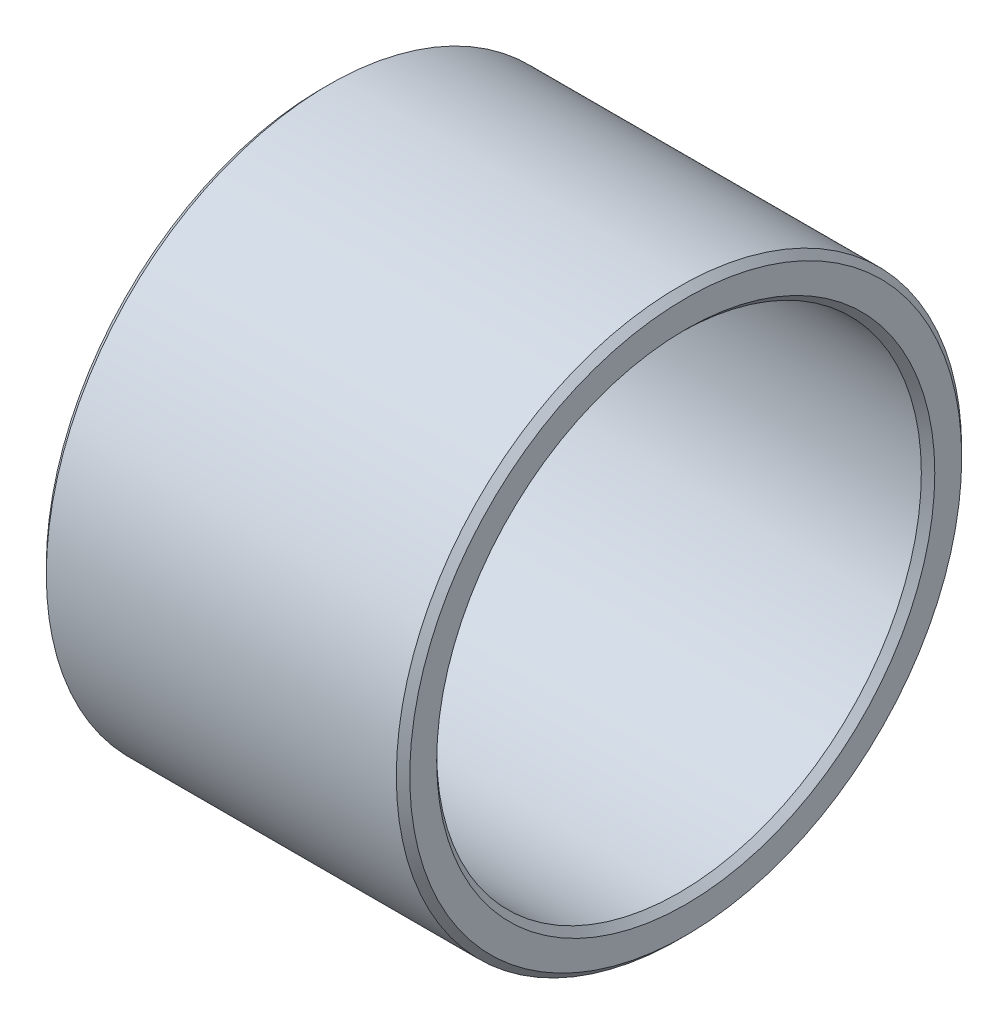
SolidWorks part; units mm, degrees
material "普通碳钢"
ref_plane "前视基准面" through (0, 0, 0) normal (0, 0, 1) x (1, 0, 0)
ref_plane "上视基准面" through (0, 0, 0) normal (0, 1, 0) x (1, 0, 0)
ref_plane "右视基准面" through (0, 0, 0) normal (1, 0, 0) x (0, 0, -1)
sketch "草图1" plane through (-4266.4235, -24.9434, -7335.5645) normal (0, -1, 0.0033) x (-1, 0, 0)
  line L0 (-4113.0475, -7413.9832) -> (-4247.4498, -7413.9832) construction
  line L1 (-4113.0475, -7441.4832) -> (-4113.0475, -7386.4832) construction
  line L3 (-4203.1784, -7392.9832) -> (-4230.1784, -7392.9832)
  line L4 (-4203.1784, -7392.9832) -> (-4203.1784, -7395.9832)
  line L5 (-4203.1784, -7395.9832) -> (-4230.1784, -7395.9832)
  line L6 (-4230.1784, -7392.9832) -> (-4230.1784, -7395.9832)
  line L7 (-4230.1784, -7433.9832) -> (-4230.1784, -7393.9832) construction
  dimension "D1" = 18
  dimension "D2" = 3
  dimension "D3" = 27
revolve "旋转1" add sketch "草图1" angle 360 about L0
chamfer "倒角1" distance 0.5 angle 45 4 edges at (-63.2451, -0.7621, 99.3793) (-63.2451, -0.7621, 96.3793) (-36.2451, -0.7621, 96.3793) (-36.2451, -0.7621, 99.3793)
